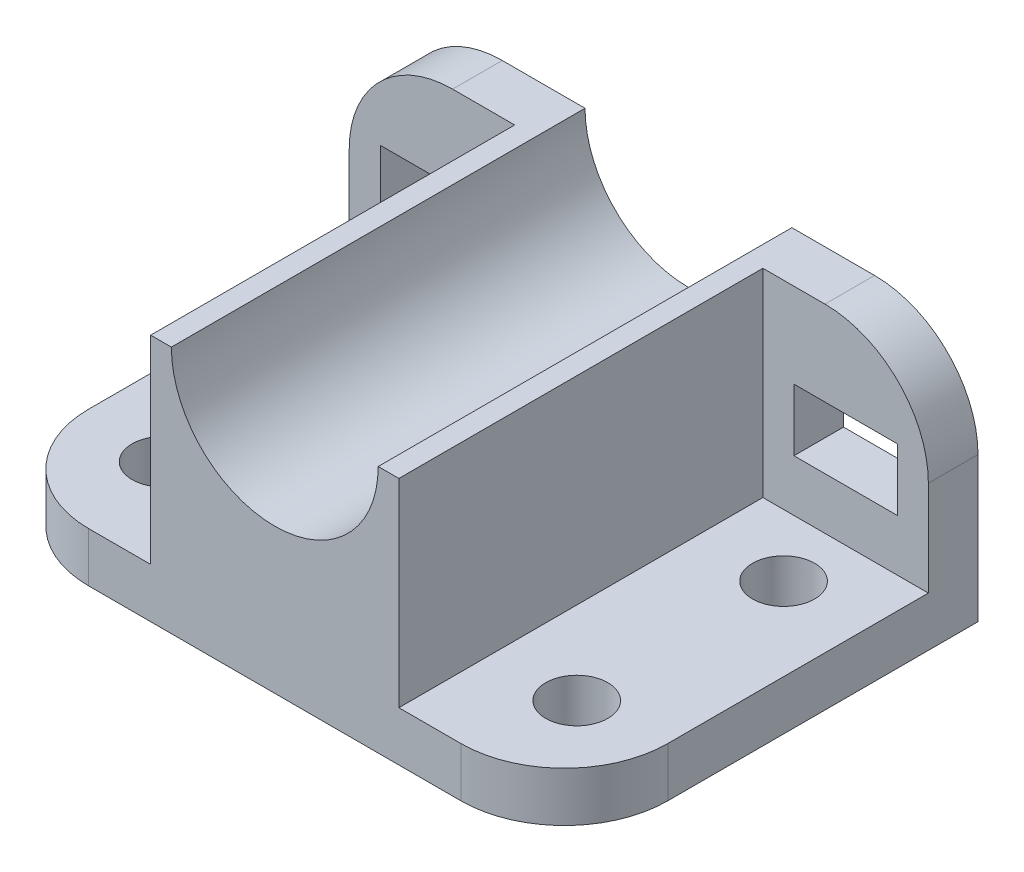
SolidWorks part; units mm, degrees
ref_plane "Front Plane" through (0, 0, 0) normal (0, 0, 1) x (1, 0, 0)
ref_plane "Top Plane" through (0, 0, 0) normal (0, 1, 0) x (1, 0, 0)
ref_plane "Right Plane" through (0, 0, 0) normal (1, 0, 0) x (0, 0, -1)
sketch "Sketch1" plane through (0, 0, 0) normal (0, 1, 0) x (1, 0, 0)
  line L1 (-70, 50) -> (70, 50)
  line L2 (-70, 50) -> (-70, -25)
  line L3 (-45, -50) -> (45, -50)
  line L4 (70, 50) -> (70, -25)
  line L5 (-70, 50) -> (70, -50) construction
  line L6 (-70, -50) -> (70, 50) construction
  arc A0 (45, -50) -> (70, -25) centre (45, -25) ccw
  arc A1 (-45, -50) -> (-70, -25) centre (-45, -25) cw
  point P0 (0, 0)
  dimension "D3" = 25
  dimension "D1" = 140
  dimension "D2" = 100
extrude "Boss-Extrude2" add sketch "Sketch1" along normal blind 12
sketch "Sketch2" plane through (0, 0, -50) normal (0, 0, -1) x (-1, 0, 0)
  line L0 (-70, 12) -> (-70, 35)
  line L1 (-45, 60) -> (45, 60)
  line L2 (70, 35) -> (70, 12)
  line L3 (-70, 12) -> (70, 12) construction
  line L4 (-70, 12) -> (70, 12)
  arc A0 (70, 35) -> (45, 60) centre (45, 35) ccw
  arc A1 (-70, 35) -> (-45, 60) centre (-45, 35) cw
  point P10 (-70, 60)
  dimension "D2" = 25
  dimension "D1" = 48
extrude "Boss-Extrude3" add sketch "Sketch2" against normal blind 12
sketch "Sketch4" plane through (0, 0, -50) normal (0, 0, -1) x (-1, 0, 0)
  line L0 (0, 35) -> (0, -29.5932) construction
  line L1 (-25, 60) -> (-30, 60)
  line L2 (45, 60) -> (-45, 60) construction
  line L3 (-30, 60) -> (-30, 12)
  line L4 (45, 12) -> (-45, 12) construction
  line L5 (-30, 12) -> (30, 12)
  line L6 (-70, 12) -> (70, 12) construction
  line L7 (30, 12) -> (30, 60)
  line L8 (30, 60) -> (25, 60)
  arc A0 (-25, 60) -> (25, 60) centre (0, 60) ccw
  dimension "D2" = 50
  dimension "D1" = 5
  dimension "D3" = 5
extrude "Boss-Extrude6" add sketch "Sketch4" against normal blind 100
sketch "Sketch5" plane through (0, 0, -38) normal (0, 0, 1) x (1, 0, 0)
  line L0 (-25, 60) -> (25, 60) construction
  circle A0 centre (0, 60) radius 25
  dimension "D1" = 50
extrude "Cut-Extrude1" cut sketch "Sketch5" against normal blind 100
sketch "Sketch7" plane through (0, 12, 0) normal (0, 1, 0) x (1, 0, 0)
  line L0 (70, 38) -> (30, 38) construction
  line L1 (0, 61.228) -> (0, -57.5429) construction
  circle A0 centre (50, 23) radius 7.5
  dimension "D1" = 15
  dimension "D2" = 15
  dimension "D3" = 50
extrude "Cut-Extrude2" cut sketch "Sketch7" against normal blind 100
pattern_linear "LPattern2" count 2 spacing 50 along (0, 0, 1) of "Cut-Extrude2"
pattern_linear "LPattern5" count 2 spacing 100 along (-1, 0, 0) of "Cut-Extrude2"
pattern_linear "LPattern6" count 2 spacing 50 along (0, 0, 1) of "LPattern5"
sketch "Sketch8" plane through (0, 0, -38) normal (0, 0, 1) x (1, 0, 0)
  line L0 (0, 98.3028) -> (0, -32.5664) construction
  line L1 (70, 12) -> (45, 12) construction
  line L2 (37.5, 39.5) -> (62.5, 39.5)
  line L3 (37.5, 39.5) -> (37.5, 24.5)
  line L4 (37.5, 24.5) -> (62.5, 24.5)
  line L5 (62.5, 39.5) -> (62.5, 24.5)
  line L6 (-62.5, 39.5) -> (-62.5, 24.5)
  line L7 (-37.5, 24.5) -> (-62.5, 24.5)
  line L8 (-37.5, 39.5) -> (-37.5, 24.5)
  line L9 (-37.5, 39.5) -> (-62.5, 39.5)
  dimension "D1" = 25
  dimension "D2" = 15
  dimension "D3" = 12.5
  dimension "D4" = 7.5
extrude "Cut-Extrude3" cut sketch "Sketch8" against normal blind 100
